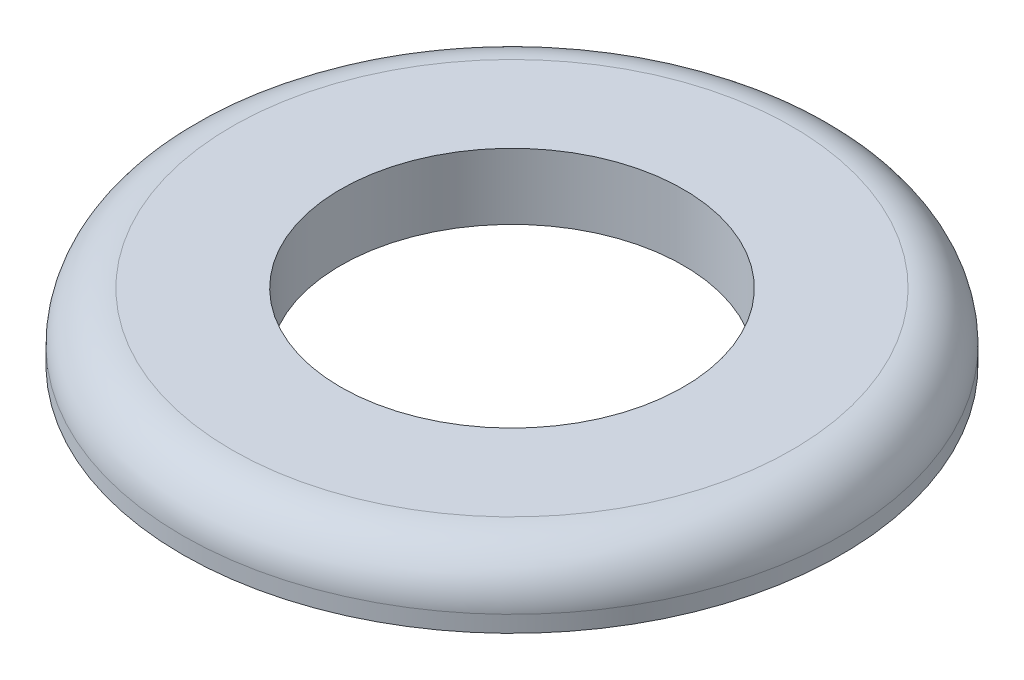
SolidWorks part; units mm, degrees
material "AISI 304"
ref_plane "Front Plane" through (0, 0, 0) normal (0, 0, 1) x (1, 0, 0)
ref_plane "Top Plane" through (0, 0, 0) normal (0, 1, 0) x (1, 0, 0)
ref_plane "Right Plane" through (0, 0, 0) normal (1, 0, 0) x (0, 0, -1)
sketch "Sketch1" plane through (0, 0, 0) normal (0, 1, 0) x (1, 0, 0)
  circle A0 centre (0, 0) radius 5
  circle A1 centre (0, 0) radius 2.6
  dimension "D1" = 5.2
  dimension "D2" = 10
extrude "Boss-Extrude1" add sketch "Sketch1" along normal blind 1
fillet "Fillet1" radius 0.75 1 edges at (0, 1, 5)
